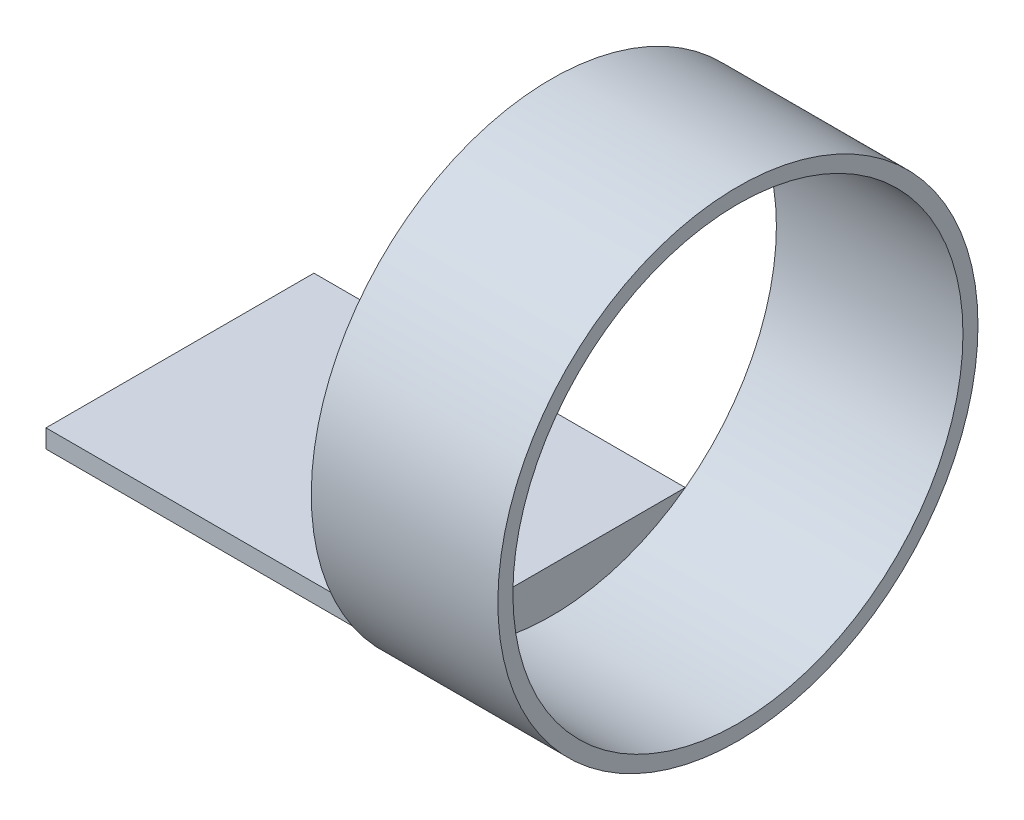
SolidWorks part; units mm, degrees
ref_plane "Front Plane" through (0, 0, 0) normal (0, 0, 1) x (1, 0, 0)
ref_plane "Top Plane" through (0, 0, 0) normal (0, 1, 0) x (1, 0, 0)
ref_plane "Right Plane" through (0, 0, 0) normal (1, 0, 0) x (0, 0, -1)
sketch "Sketch1" plane through (0, 0, 0) normal (1, 0, 0) x (0, 0, -1)
  circle A0 centre (0, 0) radius 27.15
extrude "Boss-Extrude1" add sketch "Sketch1" along normal blind 21.1
sketch "Sketch2" plane through (21.1, 0, 0) normal (1, 0, 0) x (0, 0, -1)
  circle A0 centre (0, 0) radius 25.45
extrude "Cut-Extrude1" cut sketch "Sketch2" against normal blind 21.1
sketch "Sketch3" plane through (0, 0, 0) normal (-1, 0, 0) x (0, 0, 1)
  line L0 (0, -25.45) -> (0, -20.45) construction
  line L3 (0, -20.45) -> (-15.1493, -20.45)
  line L5 (0, -20.45) -> (15.1493, -20.45)
  line L7 (-15.1493, -20.45) -> (-15.1493, -22.5305)
  line L9 (15.1493, -20.45) -> (15.1493, -22.5305)
  circle A3 centre (0, 0) radius 25.45 construction
  circle A4 centre (0, 0) radius 27.15 construction
  arc A5 (15.1493, -22.5305) -> (-15.1493, -22.5305) centre (0, 0) cw
  point P13 (0, 0)
  dimension "D1" = 5
extrude "Boss-Extrude3" add sketch "Sketch3" along normal blind 42
